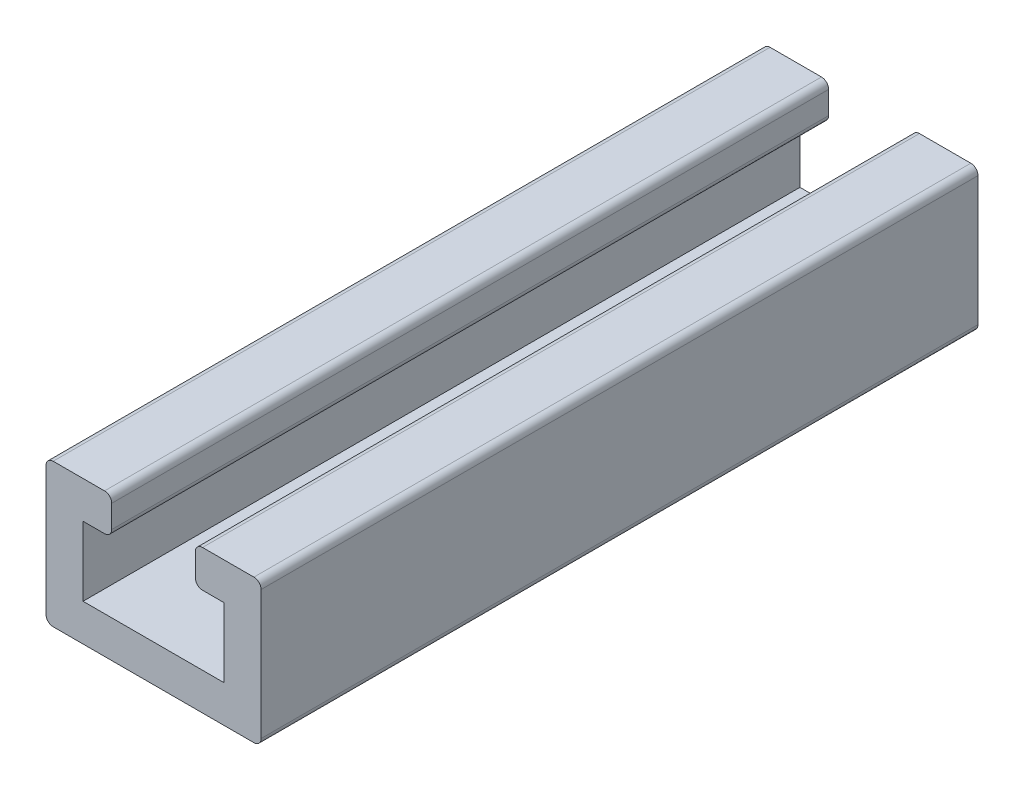
SolidWorks part; units mm, degrees
ref_plane "前视基准面" through (0, 0, 0) normal (0, 0, 1) x (1, 0, 0)
ref_plane "上视基准面" through (0, 0, 0) normal (0, 1, 0) x (1, 0, 0)
ref_plane "右视基准面" through (0, 0, 0) normal (1, 0, 0) x (0, 0, -1)
sketch "草图1" plane through (0, 0, 0) normal (0, 0, 1) x (1, 0, 0)
  line L0 (-28.4271, 7.6858) -> (-20.0271, 7.6858)
  line L1 (-19.7271, 7.9858) -> (-19.7271, 13.3858)
  line L2 (-20.0271, 13.6858) -> (-22.1771, 13.6858)
  line L3 (-22.4771, 13.3858) -> (-22.4771, 12.4358)
  line L4 (-22.1771, 12.1358) -> (-21.2771, 12.1358)
  line L5 (-21.2771, 12.1358) -> (-21.2771, 9.2358)
  line L6 (-24.2271, 7.6858) -> (-24.2271, 15.293) construction
  line L7 (-21.2771, 9.2358) -> (-27.1771, 9.2358)
  line L8 (-27.1771, 12.1358) -> (-27.1771, 9.2358)
  line L9 (-26.2771, 12.1358) -> (-27.1771, 12.1358)
  line L10 (-25.9771, 13.3858) -> (-25.9771, 12.4358)
  line L11 (-28.4271, 13.6858) -> (-26.2771, 13.6858)
  line L12 (-28.7271, 7.9858) -> (-28.7271, 13.3858)
  arc A0 (-20.0271, 7.6858) -> (-19.7271, 7.9858) centre (-20.0271, 7.9858) ccw
  arc A1 (-19.7271, 13.3858) -> (-20.0271, 13.6858) centre (-20.0271, 13.3858) ccw
  arc A2 (-22.1771, 12.1358) -> (-22.4771, 12.4358) centre (-22.1771, 12.4358) cw
  arc A3 (-22.1771, 13.6858) -> (-22.4771, 13.3858) centre (-22.1771, 13.3858) ccw
  arc A4 (-26.2771, 13.6858) -> (-25.9771, 13.3858) centre (-26.2771, 13.3858) cw
  arc A5 (-26.2771, 12.1358) -> (-25.9771, 12.4358) centre (-26.2771, 12.4358) ccw
  arc A6 (-28.7271, 13.3858) -> (-28.4271, 13.6858) centre (-28.4271, 13.3858) cw
  arc A7 (-28.4271, 7.6858) -> (-28.7271, 7.9858) centre (-28.4271, 7.9858) cw
  point P30 (-24.2271, 9.2358)
  dimension "D1" = 0.3
extrude "凸台-拉伸1" add sketch "草图1" along normal blind 30
